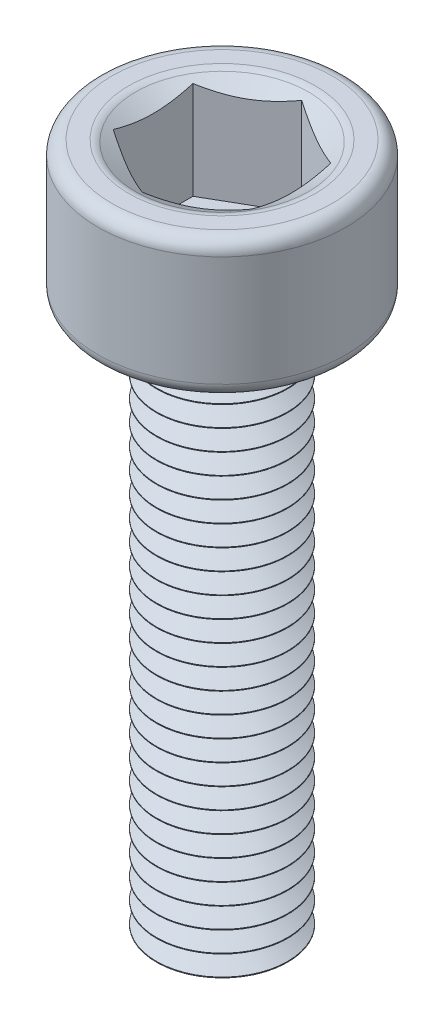
SolidWorks part; units mm, degrees
material "Plain Carbon Steel"
ref_plane "Front Plane" through (0, 0, 0) normal (0, 0, 1) x (1, 0, 0)
ref_plane "Top Plane" through (0, 0, 0) normal (0, 1, 0) x (1, 0, 0)
ref_plane "Right Plane" through (0, 0, 0) normal (1, 0, 0) x (0, 0, -1)
sketch "Sketch1" plane through (0, 0, 0) normal (0, 0, 1) x (1, 0, 0)
  line L0 (0, 2) -> (0, -8)
  line L1 (0, 2) -> (1.6, 2)
  line L2 (0, -8) -> (0.95, -8)
  line L3 (0.95, -8) -> (0.95, 0)
  line L4 (0.95, 0) -> (0, 0) construction
  line L5 (1.8, 1.8) -> (1.8, 0.2)
  line L6 (1.6, 0) -> (0.95, 0)
  arc A0 (1.6, 2) -> (1.8, 1.8) centre (1.6, 1.8) cw
  arc A1 (1.8, 0.2) -> (1.6, 0) centre (1.6, 0.2) cw
  dimension "D5" = 0.2
  dimension "D1" = 10
  dimension "D2" = 2
  dimension "D3" = 0.95
  dimension "D4" = 1.8
revolve "Revolve1" add sketch "Sketch1" angle 360 about L0
sketch "Sketch2" plane through (0, 2, 0) normal (0, 1, 0) x (1, 0, 0)
  line L1 (1, 0.5774) -> (0, 1.1547)
  line L2 (0, 1.1547) -> (-1, 0.5774)
  line L3 (-1, 0.5774) -> (-1, -0.5774)
  line L4 (-1, -0.5774) -> (0, -1.1547)
  line L5 (0, -1.1547) -> (1, -0.5774)
  line L6 (1, -0.5774) -> (1, 0.5774)
  circle A0 centre (0, 0) radius 1 construction
  dimension "D1" = 2
extrude "Cut-Extrude1" cut sketch "Sketch2" against normal blind 1.5
sketch "Sketch3" plane through (0, 2, 0) normal (0, 1, 0) x (1, 0, 0)
  circle A0 centre (0, 0) radius 1.3
  dimension "D1" = 2.6
extrude "Cut-Extrude2" cut sketch "Sketch3" against normal blind 1 draft 60
fillet "Fillet1" radius 0.2 1 edges at (-1.3, 2, 0)
sketch "Sketch4" plane through (0, 0, 0) normal (0, 0, 1) x (1, 0, 0)
  line L0 (0, 0) -> (0, -8) construction
  line L1 (-0.95, -8) -> (0.95, -8) construction
  line L2 (0, -8) -> (0.7, -8) construction
  line L3 (0.7, -8) -> (0.9598, -8) construction
  line L4 (0.9598, -8) -> (1.2598, -8) construction
  line L5 (1.2598, -7.85) -> (1.2598, -8.15)
  line L6 (0.9598, -7.85) -> (0.9598, -8.15) construction
  line L7 (1.2598, -7.85) -> (0.9598, -7.85)
  line L8 (0.9598, -7.85) -> (0.7, -8)
  line L9 (0.7, -8) -> (0.9598, -8.15)
  line L10 (0.9598, -8.15) -> (1.2598, -8.15)
  point P12 (0.9667, -8)
  dimension "D1" = 0.3
  dimension "D2" = 60
  dimension "D3" = 0.7
revolve "Cut-Revolve1" cut sketch "Sketch4" angle 360 about L0
pattern_linear "LPattern1" count 26 spacing 0.3 along (0, 1, 0) of "Cut-Revolve1"
